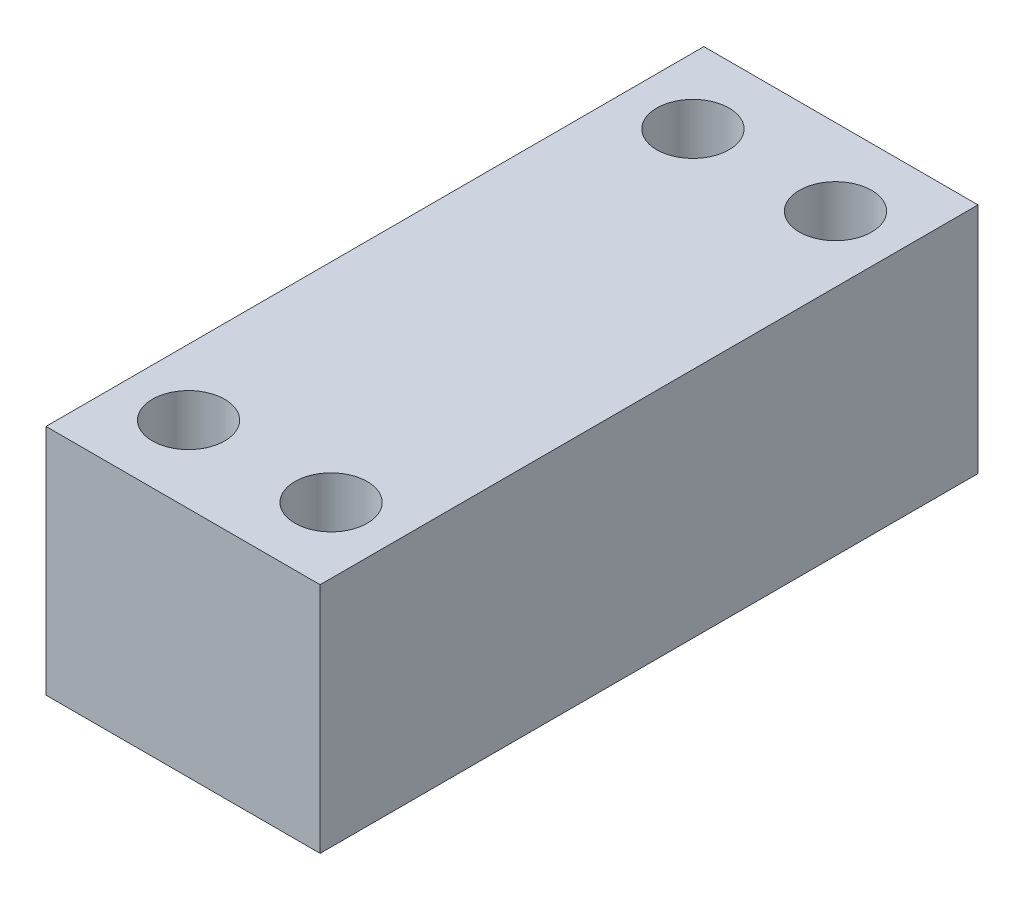
SolidWorks part; units mm, degrees
material "Delrin 2700 NC010, Low Viscosity Acetal Copolymer (SS)"
ref_plane "Front" through (0, 0, 0) normal (0, 0, 1) x (1, 0, 0)
ref_plane "Top" through (0, 0, 0) normal (0, 1, 0) x (1, 0, 0)
ref_plane "Right" through (0, 0, 0) normal (1, 0, 0) x (0, 0, -1)
sketch "Sketch1" plane through (0, 0, 0) normal (0, 1, 0) x (1, 0, 0)
  line B0 (0, 30) -> (25, 30)
  line B1 (0, 30) -> (0, -30)
  line B2 (0, -30) -> (25, -30)
  line B3 (25, 30) -> (25, -30)
  circle B4 centre (6, 23) radius 3.3
  circle B5 centre (19, 23) radius 3.3
  circle B6 centre (19, -23) radius 3.3
  circle B7 centre (6, -23) radius 3.3
sketch_block_instance "Block-BK12Spacer-1"
sketch_block "Block-BK12Spacer"
extrude "Boss-Extrude1" add sketch "Sketch1" along normal blind 21.2242
